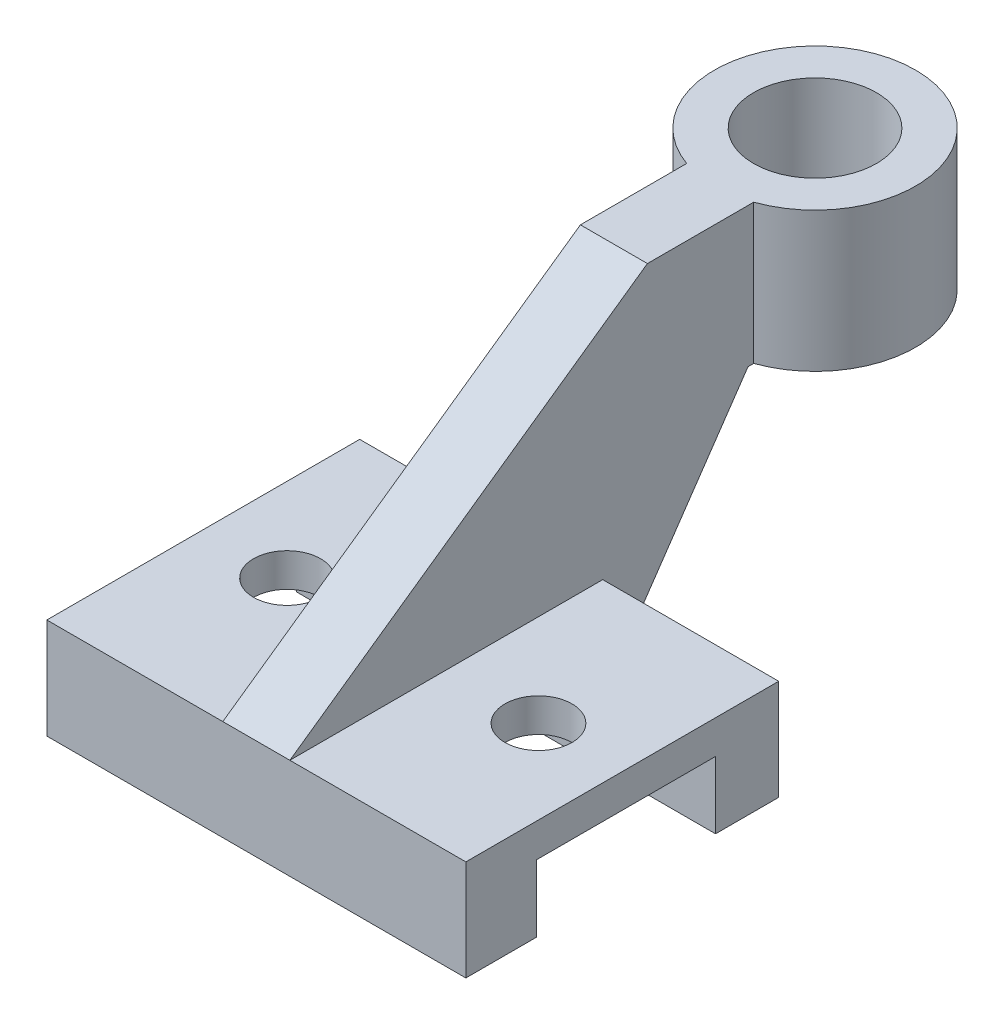
SolidWorks part; units mm, degrees
ref_plane "Front Plane" through (0, 0, 0) normal (0, 0, 1) x (1, 0, 0)
ref_plane "Top Plane" through (0, 0, 0) normal (0, 1, 0) x (1, 0, 0)
ref_plane "Right Plane" through (0, 0, 0) normal (1, 0, 0) x (0, 0, -1)
sketch "Sketch1" plane through (0, 0, 0) normal (1, 0, 0) x (0, 0, -1)
  line L0 (-1016.5319, -597.6314) -> (-694.178, -597.6314)
  line L1 (-694.178, -597.6314) -> (-694.178, -292.8314)
  line L2 (-694.178, -292.8314) -> (118.622, -292.8314)
  line L3 (118.622, -292.8314) -> (118.622, -597.6314)
  line L4 (-1016.5319, -597.6314) -> (-1016.5319, -140.4314)
  line L5 (-1016.5319, -140.4314) -> (405.8681, -140.4314)
  line L6 (405.8681, -140.4314) -> (405.8681, -597.6314)
  line L7 (405.8681, -597.6314) -> (118.622, -597.6314)
  dimension "D1" = 304.8
  dimension "D2" = 457.2
  dimension "D3" = 304.8
  dimension "D4" = 1422.4
  dimension "D5" = 812.8
  dimension "D6" = 287.2461
extrude "Boss-Extrude1" add sketch "Sketch1" along normal blind 1905 contours L7 L3 L2 L1 L0 L4 L5 L6
ref_plane "Plane1" through (0, 1002.5686, 0) normal (0, 1, 0) x (1, 0, 0)
sketch "Sketch6" plane through (0, 1002.5686, 0) normal (0, 1, 0) x (1, 0, 0)
  line L0 (1905, -1016.5319) -> (0, -1016.5319) construction
  circle A0 centre (952.5, 1523.4681) radius 457.2
  circle A1 centre (952.5, 1523.4681) radius 279.4
  point P5 (952.5, -1016.5319)
  dimension "D1" = 914.4
  dimension "D2" = 558.8
  dimension "D3" = 2540
extrude "Boss-Extrude2" add sketch "Sketch6" against normal blind 635 separate body
sketch "Sketch8" plane through (0, 1002.5686, 0) normal (0, 1, 0) x (1, 0, 0)
  line L1 (952.5, 1066.2681) -> (952.5, 609.0681)
ref_plane "Plane2" through (952.5, 0, 0) normal (1, 0, 0) x (0, 0, -1)
sketch "Sketch10" plane through (952.5, 0, 0) normal (1, 0, 0) x (0, 0, -1)
  line L0 (609.0681, 1002.5686) -> (-1016.5319, -140.4314)
  line L1 (1066.2681, 1002.5686) -> (1066.2681, 367.5686)
  line L2 (1066.2681, 367.5686) -> (405.8681, -597.6314)
  line L3 (609.0681, 1002.5686) -> (1066.2681, 1002.5686)
  line L4 (-1016.5319, -140.4314) -> (405.8681, -140.4314)
  line L5 (405.8681, -140.4314) -> (405.8681, -597.6314)
extrude "Boss-Extrude3" add sketch "Sketch10" along normal blind 152.4 and the other way blind 152.4
sketch "Sketch11" plane through (0, -140.4314, 0) normal (0, 1, 0) x (1, 0, 0)
  line L0 (800.1, -1016.5319) -> (0, -1016.5319) construction
  line L1 (1905, -1016.5319) -> (1104.9, -1016.5319) construction
  line L2 (1905, -1016.5319) -> (1905, 405.8681) construction
  line L3 (0, -694.178) -> (0, 118.622) construction
  circle A0 centre (1524, -305.3319) radius 152.4
  circle A1 centre (381, -305.3319) radius 152.4
  dimension "D1" = 711.2
  dimension "D3" = 304.8
  dimension "D2" = 381
  dimension "D4" = 381
  dimension "D5" = 711.2
extrude "Cut-Extrude1" cut sketch "Sketch11" against normal up to next (152.4 mm away)
sketch "Sketch12" plane through (0, 0, -1066.2681) normal (0, 0, -1) x (-1, 0, 0)
  line L0 (-1104.9, 1002.5686) -> (-800.1, 1002.5686)
  line L1 (-800.1, 1002.5686) -> (-800.1, 367.5686)
  line L2 (-800.1, 367.5686) -> (-1104.9, 367.5686)
  line L3 (-1104.9, 367.5686) -> (-1104.9, 1002.5686)
extrude "Boss-Extrude6" add sketch "Sketch12" along normal blind 152.4
sketch "Sketch7" plane through (0, 1002.5686, 0) normal (0, 1, 0) x (1, 0, 0)
